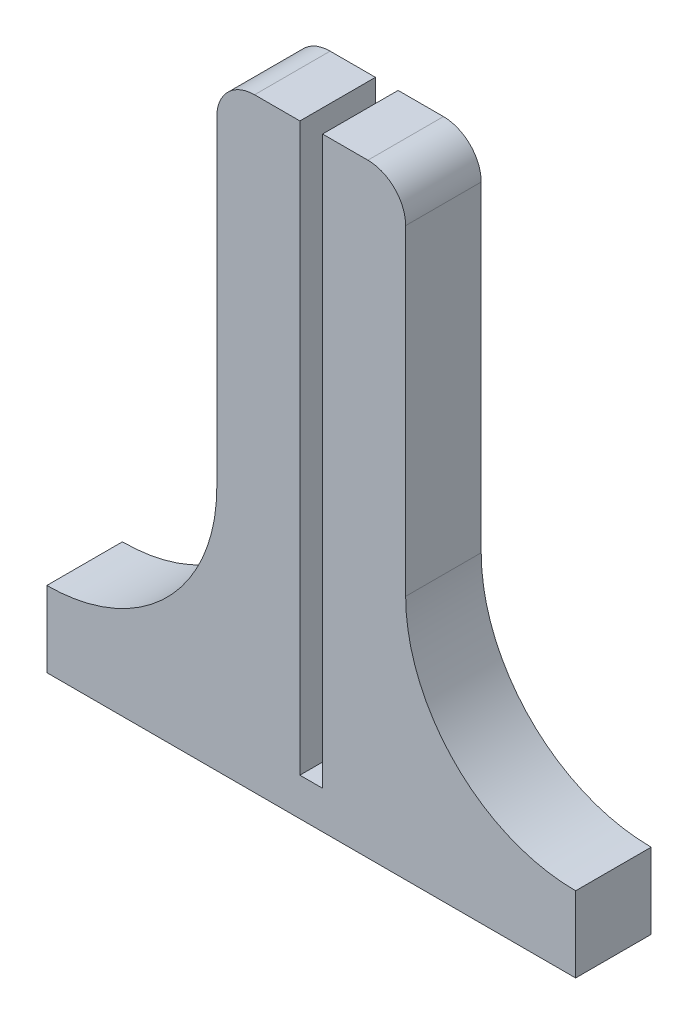
SolidWorks part; units mm, degrees
ref_plane "Plan de face" through (0, 0, 0) normal (0, 0, 1) x (1, 0, 0)
ref_plane "Plan de dessus" through (0, 0, 0) normal (0, 1, 0) x (1, 0, 0)
ref_plane "Plan de droite" through (0, 0, 0) normal (1, 0, 0) x (0, 0, -1)
sketch "Esquisse1" plane through (0, 0, 0) normal (0, 0, 1) x (1, 0, 0)
  line L0 (-70, 0) -> (70, 0)
  line L1 (70, 0) -> (70, 20)
  line L2 (25, 65) -> (25, 160)
  line L3 (25, 160) -> (-25, 160)
  line L4 (0, -36.4078) -> (0, 122.8519) construction
  line L5 (-70, 0) -> (-70, 20)
  line L6 (-25, 65) -> (-25, 160)
  arc A0 (70, 20) -> (25, 65) centre (70, 65) cw
  arc A1 (-70, 20) -> (-25, 65) centre (-70, 65) ccw
  point P4 (0, 0)
  point P15 (0, 160)
  dimension "D1" = 140
  dimension "D2" = 20
  dimension "D3" = 50
  dimension "D4" = 160
extrude "Boss.-Extru.1" add sketch "Esquisse1" along normal blind 20
fillet "Congé1" radius 10 2 edges at (-25, 160, 10) (25, 160, 10)
sketch "Esquisse2" plane through (0, 0, 20) normal (0, 0, 1) x (1, 0, 0)
  line L0 (-3, 10) -> (-3, 160)
  line L1 (-3, 10) -> (3, 10)
  line L2 (-3, 160) -> (3, 160)
  line L3 (3, 10) -> (3, 160)
  line L4 (-3, 10) -> (3, 160) construction
  line L5 (-3, 160) -> (3, 10) construction
  line L6 (-70, 0) -> (70, 0) construction
  line L7 (15, 160) -> (-15, 160) construction
  point P1 (0, 85)
  point P2 (0, 10)
  dimension "D1" = 6
  dimension "D2" = 10
extrude "Enlèv. mat.-Extru.1" cut sketch "Esquisse2" against normal blind 20
sketch "Esquisse3" plane through (-25, 0, 0) normal (-1, 0, 0) x (0, 0, 1)
  line L0 (10, 150) -> (10, 65) construction
  line L1 (20, 150) -> (0, 150) construction
  line L2 (20, 65) -> (0, 65) construction
  text T0 "Innovation Lab" font "Calibri" height 3.5
extrude "Enlèv. mat.-Extru.2" cut sketch "Esquisse3" against normal blind 0.6
